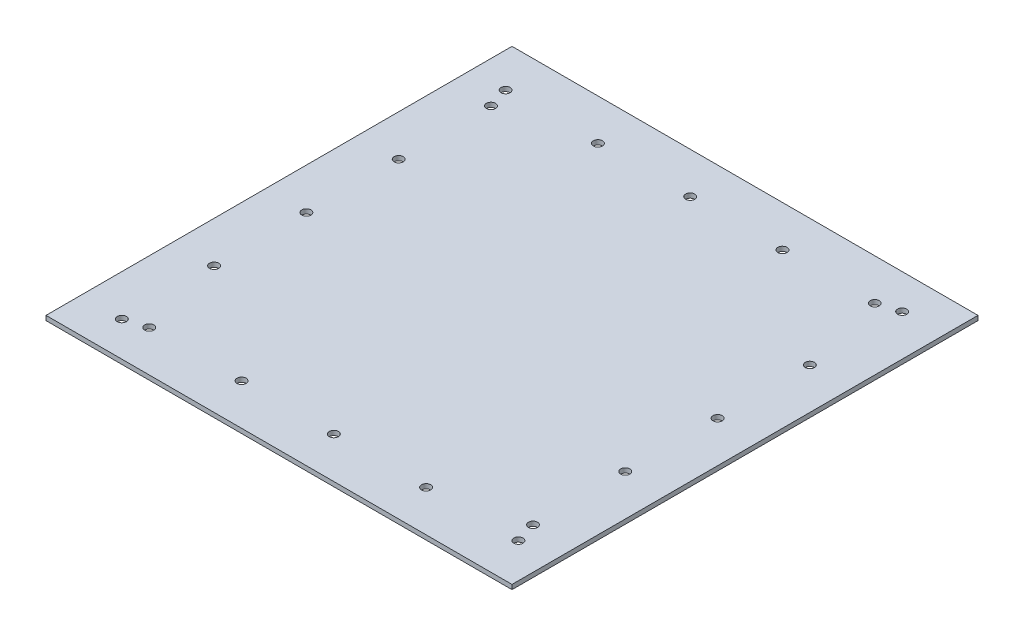
SolidWorks part; units mm, degrees
material "Silicon Rubber"
ref_plane "Front Plane" through (0, 0, 0) normal (0, 0, 1) x (1, 0, 0)
ref_plane "Top Plane" through (0, 0, 0) normal (0, 1, 0) x (1, 0, 0)
ref_plane "Right Plane" through (0, 0, 0) normal (1, 0, 0) x (0, 0, -1)
sketch "Sketch1" plane through (0, 0, 0) normal (0, 1, 0) x (1, 0, 0)
  line L1 (-255, -255) -> (255, -255)
  line L2 (-255, -255) -> (-255, 255)
  line L3 (-255, 255) -> (255, 255)
  line L4 (255, -255) -> (255, 255)
  line L5 (-255, -255) -> (255, 255) construction
  line L6 (-255, 255) -> (255, -255) construction
  point P0 (0, 0)
  dimension "D1" = 510
  dimension "D2" = 510
extrude "Boss-Extrude1" add sketch "Sketch1" along normal blind 5
sketch "Sketch3" plane through (0, 0, 0) normal (0, -1, 0) x (1, 0, 0)
  line L1 (225, -225) -> (-225, -225) construction
  line L2 (225, -225) -> (225, 225) construction
  line L3 (225, 225) -> (-225, 225) construction
  line L4 (-225, -225) -> (-225, 225) construction
  line L5 (225, -225) -> (-225, 225) construction
  line L6 (225, 225) -> (-225, -225) construction
  line L7 (-255, 255) -> (255, -255) construction
  line L8 (210, 210) -> (-210, 210) construction
  line L9 (-210, -210) -> (-210, 210) construction
  line L10 (210, -210) -> (-210, -210) construction
  line L11 (210, -210) -> (210, 210) construction
  circle A0 centre (217, 210) radius 5
  circle A1 centre (116, 210) radius 5
  circle A2 centre (15, 210) radius 5
  circle A3 centre (-86, 210) radius 5
  circle A4 centre (-187, 210) radius 5
  circle A5 centre (-210, 217) radius 5
  circle A6 centre (-210, 116) radius 5
  circle A7 centre (-210, 15) radius 5
  circle A8 centre (-210, -86) radius 5
  circle A9 centre (-210, -187) radius 5
  circle A10 centre (-217, -210) radius 5
  circle A11 centre (-116, -210) radius 5
  circle A12 centre (-15, -210) radius 5
  circle A13 centre (86, -210) radius 5
  circle A14 centre (187, -210) radius 5
  circle A15 centre (210, -217) radius 5
  circle A16 centre (210, -116) radius 5
  circle A17 centre (210, -15) radius 5
  circle A18 centre (210, 86) radius 5
  circle A19 centre (210, 187) radius 5
  point P0 (0, 0)
  dimension "D1" = 450
  dimension "D5" = 5
  dimension "D2" = 8
  dimension "D4" = 8
  dimension "D6" = 8
  dimension "D8" = 8
  dimension "D3" = 5
  dimension "D7" = 5
  dimension "D9" = 5
extrude "Cut-Extrude1" cut sketch "Sketch3" against normal through all
